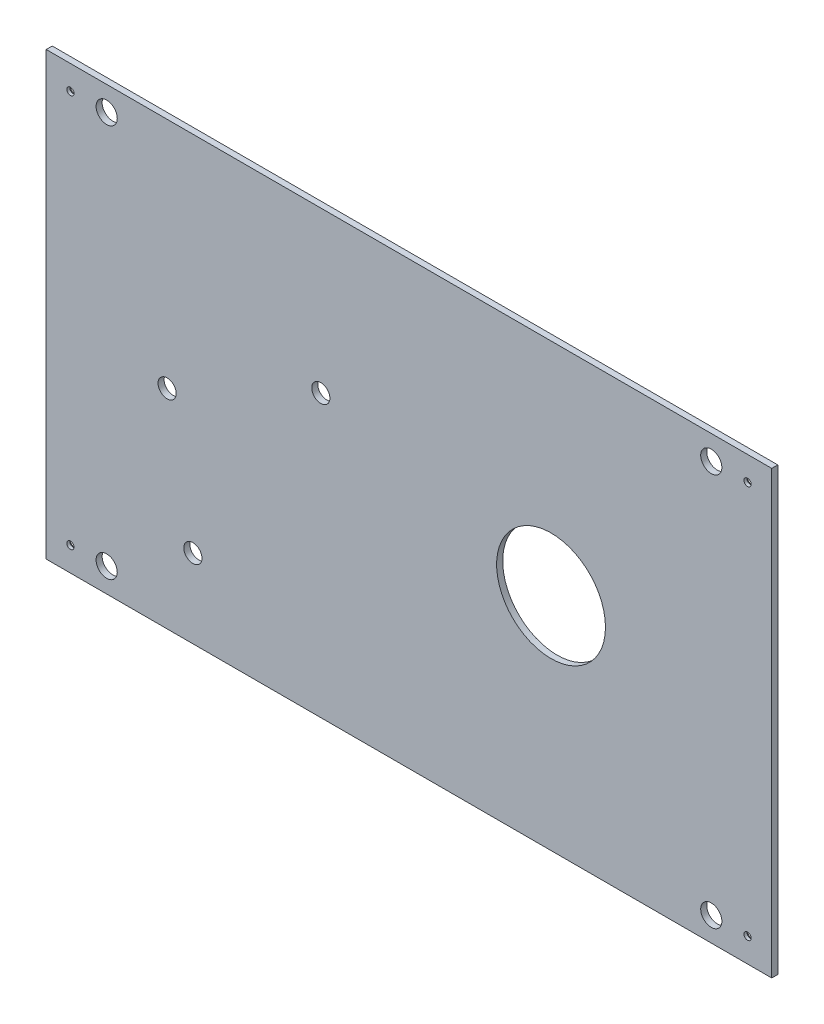
SolidWorks part; units mm, degrees
material "Сталь ШХ15 ГОСТ 801-78"
ref_plane "Plane1" through (0, 0, 0) normal (0, 0, 1) x (1, 0, 0)
ref_plane "Plane2" through (0, 0, 0) normal (0, 1, 0) x (1, 0, 0)
ref_plane "Plane3" through (0, 0, 0) normal (1, 0, 0) x (0, 0, -1)
sketch "Эскиз1" plane through (0, 0, 0) normal (0, 0, 1) x (1, 0, 0)
  line L0 (0, 73) -> (240, 73) construction
  line L1 (0, 0) -> (240, 0)
  line L2 (0, 0) -> (0, 146)
  line L3 (0, 146) -> (240, 146)
  line L4 (240, 0) -> (240, 146)
  line L5 (120, 146) -> (120, 0) construction
  circle A0 centre (79.7654, 26) radius 11
  circle A1 centre (48.5154, 26) radius 3
  circle A2 centre (40, 68.9133) radius 3
  circle A3 centre (90.832, 93) radius 3
  circle A4 centre (167, 73) radius 18
  circle A5 centre (20, 138) radius 3.5
  circle A6 centre (20, 8) radius 3.5
  circle A7 centre (220, 8) radius 3.5
  circle A8 centre (220, 138) radius 3.5
  circle A9 centre (8, 138) radius 2.5
  circle A10 centre (232, 138) radius 2.5
  circle A11 centre (8, 8) radius 2.5
  circle A12 centre (232, 8) radius 2.5
  point P23 (0, 0)
  point P36 (0, 0)
  dimension "D3" = 22
  dimension "D4" = 53
  dimension "D5" = 6
  dimension "D6" = 31.25
  dimension "D9" = 73
  dimension "D10" = 36
  dimension "D19" = 7
  dimension "D20" = 5
  dimension "D2" = 78.75
  dimension "D7" = 43.75
  dimension "D8" = 56.25
  dimension "D11" = 73
  dimension "D12" = 146
  dimension "D13" = 240
  dimension "D14" = 40
  dimension "D15" = 26
  dimension "D16" = 26
  dimension "D17" = 8
  dimension "D18" = 20
  dimension "D21" = 8
extrude "Бобышка-Вытянуть1" add sketch "Эскиз1" along normal blind 2
hole_wizard "Зенковка для винта с полупотайной головкой M21" positions "Эскиз4" profile "Эскиз5" countersink size "M2" standard "ISO" end condition through all
sketch "Эскиз4" plane through (0, 0, 0) normal (0, 0, -1) x (-1, 0, 0)
  point P0 (-232, 138)
  point P3 (-8, 138)
  point P6 (-8, 8)
  point P9 (-232, 8)
sketch "Эскиз5" plane through (232, 138, 0) normal (1, 0, 0) x (0, 1, 0)
  line L0 (0, 0) -> (0, 2)
  line L1 (0, 2) -> (1.2, 2)
  line L2 (1.2, 2) -> (1.2, 1)
  line L3 (1.2, 1) -> (2.2, 0)
  line L5 (2.2, 0) -> (0, 0)
  line L6 (-1.2, 1) -> (-2.2, 0) construction
  line L11 (0, -6.35) -> (0, 107.95) construction
  dimension "Диаметр сквозного отверстия" = 2.4
  dimension "Глубина сквозного отверстия" = 2
  dimension "Диаметр передней зенковки" = 4.4
  dimension "Угол передней зенковки" = 90
